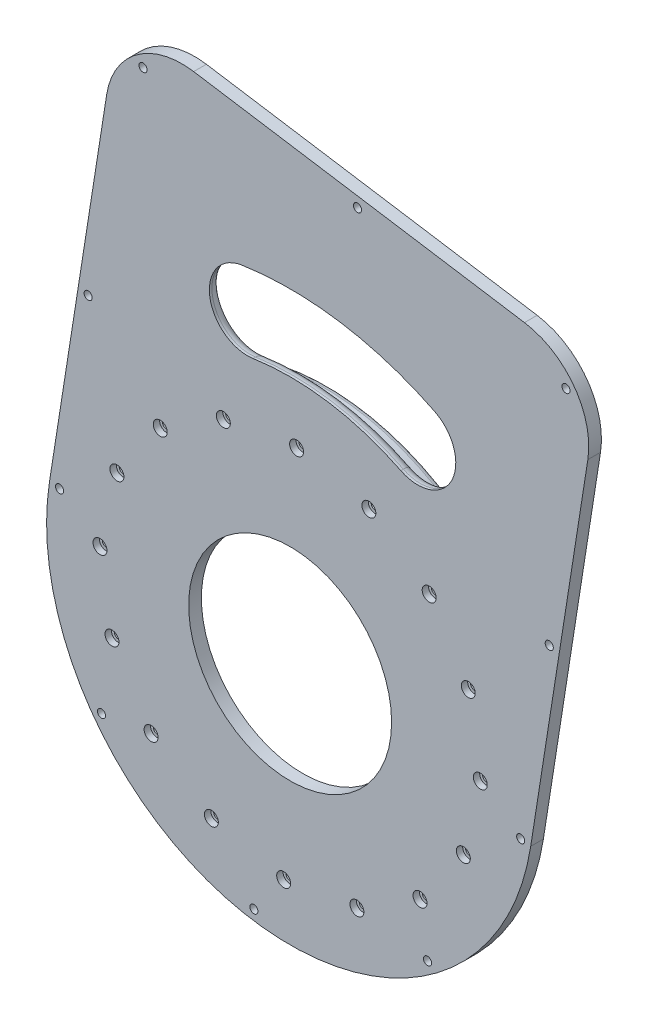
SolidWorks part; units mm, degrees
ref_plane "Front Plane" through (0, 0, 0) normal (0, 0, 1) x (1, 0, 0)
ref_plane "Top Plane" through (0, 0, 0) normal (0, 1, 0) x (1, 0, 0)
ref_plane "Right Plane" through (0, 0, 0) normal (1, 0, 0) x (0, 0, -1)
sketch "Sketch1" plane through (0, 0, 0) normal (0, 0, 1) x (1, 0, 0)
  circle A0 centre (20.1422, -37.1244) radius 84
  circle A1 centre (20.1422, -37.1244) radius 88
  circle A2 centre (20.1422, -37.1244) radius 83.5 construction
  dimension "D1" = 0.5
  dimension "D2" = 4
extrude "Boss-Extrude1" add sketch "Sketch1" along normal offset from surface (14 mm away) 4 from offset 10
sketch "Sketch2" plane through (0, 0, 4) normal (0, 0, 1) x (1, 0, 0)
  line L0 (-74.6934, -22.2176) -> (-47.5155, 150.6852)
  line L1 (-47.5155, 150.6852) -> (142.1556, 120.8716)
  line L2 (142.1556, 120.8716) -> (114.9777, -52.0312)
  line L3 (-43.7864, 39.0521) -> (-34.097, 100.6953) construction
  line L4 (-31.4107, 117.7854) -> (-22.5198, 116.3879) construction
  line L5 (20.1422, -37.1244) -> (47.3201, 135.7784) construction
  arc A0 (-74.6934, -22.2176) -> (114.9777, -52.0312) centre (20.1422, -37.1244) ccw
  circle A1 centre (20.1422, -37.1244) radius 40
  circle A2 centre (20.1422, -37.1244) radius 88 construction
  arc A3 (63.767, 50.6302) -> (5.5435, 59.7821) centre (20.1422, -37.1244) ccw
  arc A4 (77.1215, 77.4939) -> (1.0745, 89.4474) centre (20.1422, -37.1244) ccw
  arc A5 (63.767, 50.6302) -> (77.1215, 77.4939) centre (70.4442, 64.0621) ccw
  arc A6 (5.5435, 59.7821) -> (1.0745, 89.4474) centre (3.309, 74.6148) cw
  point P20 (35.3596, 59.6869)
  point P21 (40.0179, 89.323)
  dimension "D2" = 80
  dimension "D3" = 8
  dimension "D4" = 10
  dimension "D5" = 30
  dimension "D1" = 30
extrude "Boss-Extrude2" add sketch "Sketch2" against normal up to surface (5 mm away) from offset 1
sketch "Sketch3" plane through (0, 0, 0) normal (0, 0, -1) x (-1, 0, 0)
  circle A0 centre (31.0572, 17.6809) radius 1.6
  circle A1 centre (48.133, -6.084) radius 1.6
  circle A2 centre (54.8145, -34.5746) radius 1.6
  circle A3 centre (50.0845, -63.4534) radius 1.6
  circle A4 centre (34.6632, -88.3238) radius 1.6
  circle A5 centre (10.8982, -105.3996) radius 1.6
  circle A6 centre (-17.5924, -112.0811) radius 1.6
  circle A7 centre (-46.4711, -107.3511) radius 1.6
  circle A8 centre (-71.3415, -91.9297) radius 1.6
  circle A9 centre (-88.4173, -68.1648) radius 1.6
  circle A10 centre (-95.0988, -39.6742) radius 1.6
  circle A11 centre (-90.3688, -10.7954) radius 1.6
  circle A12 centre (-74.9475, 14.075) radius 1.6
  circle A13 centre (-51.1825, 31.1507) radius 1.6
  circle A14 centre (-22.692, 37.8322) radius 1.6
  circle A15 centre (6.1868, 33.1023) radius 1.6
  point P35 (-20.1422, -37.1244)
  dimension "D1" = 3.2
  dimension "D2" = 16
extrude "Cut-Extrude1" cut sketch "Sketch3" against normal up to next
fillet "Fillet1" radius 30 2 edges at (142.1556, 120.8716, 2.5) (-47.5155, 150.6852, 2.5)
sketch "Sketch4" plane through (0, 0, 5) normal (0, 0, 1) x (1, 0, 0)
  circle A0 centre (90.3688, -10.7954) radius 2.75
  circle A1 centre (95.0988, -39.6742) radius 2.75
  circle A2 centre (88.4173, -68.1648) radius 2.75
  circle A3 centre (71.3415, -91.9297) radius 2.75
  circle A4 centre (46.4711, -107.3511) radius 2.75
  circle A5 centre (17.5924, -112.0811) radius 2.75
  circle A6 centre (-10.8982, -105.3996) radius 2.75
  circle A7 centre (-34.6632, -88.3238) radius 2.75
  circle A8 centre (-50.0845, -63.4534) radius 2.75
  circle A9 centre (-54.8145, -34.5746) radius 2.75
  circle A10 centre (-48.133, -6.084) radius 2.75
  circle A11 centre (-31.0572, 17.6809) radius 2.75
  circle A12 centre (-6.1868, 33.1023) radius 2.75
  circle A13 centre (22.692, 37.8322) radius 2.75
  circle A14 centre (51.1825, 31.1507) radius 2.75
  circle A15 centre (74.9475, 14.075) radius 2.75
  point P36 (20.1422, -37.1244)
  dimension "D1" = 5.5
  dimension "D2" = 16
extrude "Cut-Extrude2" cut sketch "Sketch4" against normal blind 2.5
fillet "Fillet2" radius 2 1 edges at (108.1422, -37.1244, 0)
fillet "Fillet3" radius 2 1 edges at (108.1422, -37.1244, -10)
sketch "Sketch5" plane through (0, 0, 5) normal (0, 0, 1) x (1, 0, 0)
  circle A0 centre (128.8777, 111.2008) radius 1.6
  circle A1 centre (122.286, 20.2232) radius 1.6
  circle A2 centre (111.0263, -51.4101) radius 1.6
  circle A3 centre (74.3054, -111.4907) radius 1.6
  circle A4 centre (5.8564, -128.0085) radius 1.6
  circle A5 centre (-54.2241, -91.2876) radius 1.6
  circle A6 centre (-70.7419, -22.8387) radius 1.6
  circle A7 centre (-59.4822, 48.7946) radius 1.6
  circle A8 centre (-37.8448, 137.4073) radius 1.6
  circle A9 centre (46.699, 131.8269) radius 1.6
  dimension "D1" = 3.2
extrude "Cut-Extrude3" cut sketch "Sketch5" against normal through all
sketch "Sketch6" plane through (0, 0, 0) normal (0, 0, -1) x (-1, 0, 0)
  circle A0 centre (-128.8777, 111.2008) radius 2.775
  circle A1 centre (-46.699, 131.8269) radius 2.775
  circle A2 centre (37.8448, 137.4073) radius 2.775
  circle A3 centre (59.4822, 48.7946) radius 2.775
  circle A4 centre (70.7419, -22.8387) radius 2.775
  circle A5 centre (54.2241, -91.2876) radius 2.775
  circle A6 centre (-5.8564, -128.0085) radius 2.775
  circle A7 centre (-74.3054, -111.4907) radius 2.775
  circle A8 centre (-111.0263, -51.4101) radius 2.775
  circle A9 centre (-122.286, 20.2232) radius 2.775
  dimension "D1" = 5.55
extrude "Cut-Extrude4" cut sketch "Sketch6" against normal offset from surface (7.5 mm away) 2.5 from offset 5
fillet "Fillet4" radius 4 4 edges at (83.8761, 57.3848, 0) (40.0179, 89.323, 0) (-11.5236, 72.3803, 0) (35.3596, 59.6869, 0)
